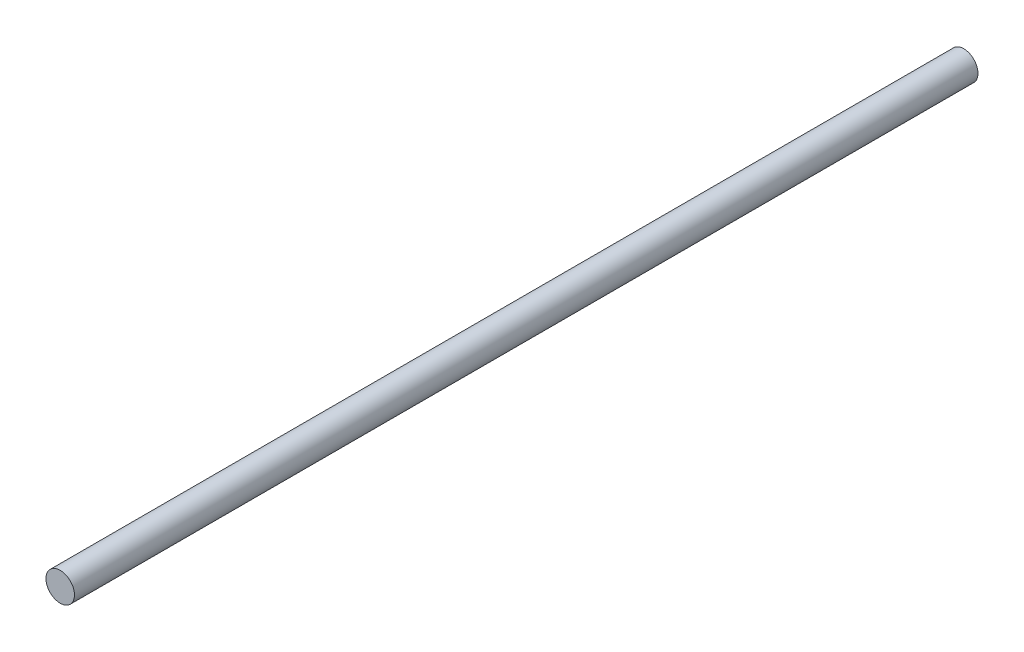
SolidWorks part; units mm, degrees
ref_plane "Ön Düzlem" through (0, 0, 0) normal (0, 0, 1) x (1, 0, 0)
ref_plane "Üst Düzlem" through (0, 0, 0) normal (0, 1, 0) x (1, 0, 0)
ref_plane "Sağ Düzlem" through (0, 0, 0) normal (1, 0, 0) x (0, 0, -1)
sketch "Çizim1" plane through (0, 0, 0) normal (0, 0, 1) x (1, 0, 0)
  circle A0 centre (0, 0) radius 3.975
  dimension "D1" = 7.95
extrude "Yükseklik-Ekstrüzyon1" add sketch "Çizim1" along normal blind 252
